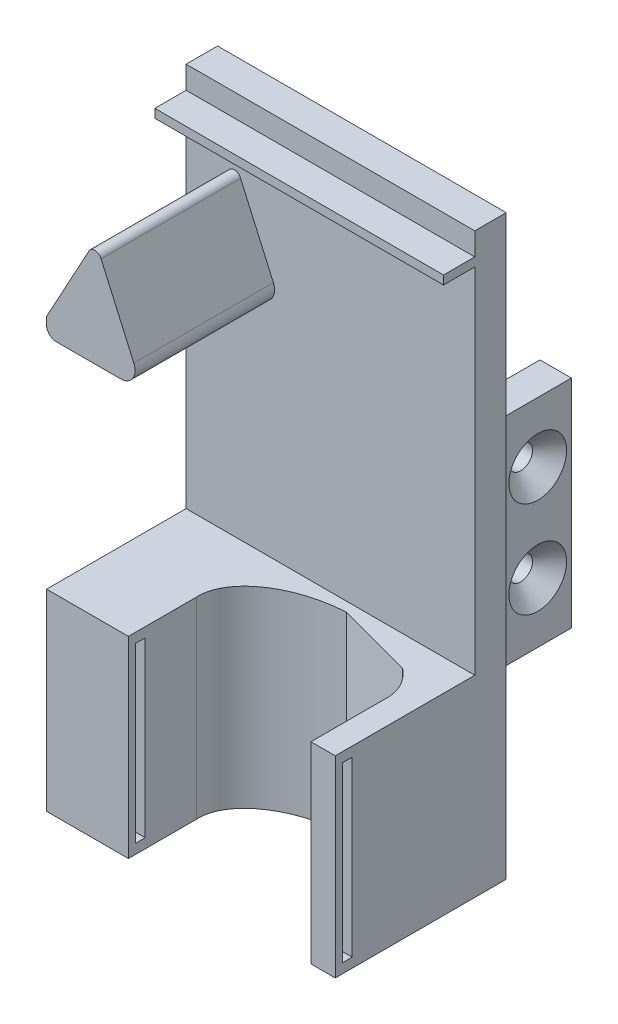
SolidWorks part; units mm, degrees
ref_plane "Front Plane" through (0, 0, 0) normal (0, 0, 1) x (1, 0, 0)
ref_plane "Top Plane" through (0, 0, 0) normal (0, 1, 0) x (1, 0, 0)
ref_plane "Right Plane" through (0, 0, 0) normal (1, 0, 0) x (0, 0, -1)
sketch "Sketch1" plane through (0, 0, 0) normal (0, 0, 1) x (1, 0, 0)
  line L1 (-30, 60) -> (30, 60)
  line L2 (-30, 60) -> (-30, -60)
  line L3 (-30, -60) -> (30, -60)
  line L4 (30, 60) -> (30, -60)
  line L5 (-30, 60) -> (30, -60) construction
  line L6 (-30, -60) -> (30, 60) construction
  point P0 (0, 0)
  dimension "D1" = 60
  dimension "D2" = 120
extrude "Boss-Extrude1" add sketch "Sketch1" along normal blind 6.54
sketch "Sketch7" plane through (0, 0, 6.54) normal (0, 0, 1) x (1, 0, 0)
  line L0 (-10, 25.5339) -> (-18.6733, 45.1016)
  line L1 (-30, 25.5339) -> (-10, 25.5339)
  line L6 (30, -60) -> (30, 60) construction
  line L15 (-21.3057, 45.0714) -> (-30, 29.1154)
  line L16 (-30, 60) -> (-30, -60) construction
  line L18 (-30, 29.1154) -> (-30, 25.5339)
  line L19 (30, 60) -> (-30, 60) construction
  arc A1 (-21.3057, 45.0714) -> (-18.6733, 45.1016) centre (-19.9839, 44.595) cw
  point P3 (-20, 46)
  dimension "D1" = 14
  dimension "D3" = 20
  dimension "D4" = 40
  dimension "D2" = 50
sketch "Sketch10" plane through (0, 0, 0) normal (0, 0, -1) x (-1, 0, 0)
  line L1 (20, 20) -> (26.54, 20)
  line L2 (-20, -25) -> (-20, 20)
  line L4 (-20, 20) -> (-26.54, 20)
  line L7 (20, -25) -> (20, 20)
  line L10 (-26.54, 20) -> (-26.54, -25)
  line L11 (-26.54, -25) -> (-20, -25)
  line L12 (26.54, 20) -> (26.54, -25)
  line L13 (26.54, -25) -> (20, -25)
  dimension "D1" = 6.54
  dimension "D2" = 20
  dimension "D3" = 6.54
  dimension "D4" = 20
  dimension "D5" = 45
  dimension "D6" = 45
extrude "Boss-Extrude5" add sketch "Sketch10" along normal blind 17
sketch "Sketch17" plane through (0, 0, 6.54) normal (0, 0, 1) x (1, 0, 0)
  line L0 (-30, 60) -> (-30, -60) construction
  line L1 (-30, -20) -> (30, -20)
  line L2 (-30, -20) -> (-30, -60)
  line L3 (-30, -60) -> (30, -60)
  line L4 (30, -20) -> (30, -60)
  line L5 (30, -60) -> (30, 60) construction
  line L6 (-30, -60) -> (30, -60) construction
  line L7 (30, 60) -> (-30, 60) construction
  dimension "D1" = 40
  dimension "D2" = 0
  dimension "D3" = 80
extrude "Boss-Extrude6" add sketch "Sketch17" along normal blind 29
sketch "Sketch18" plane through (0, -20, 0) normal (0, 1, 0) x (1, 0, 0)
  line L0 (5.335, -8.5264) -> (21.2913, -12.8258)
  line L1 (30, -35.54) -> (30, -6.54) construction
  line L2 (30, -35.54) -> (-30, -35.54) construction
  ellipse E0 centre (5.9723, -20.3092) end of major axis (24.9445, -19.283) minor radius 11.8 (5.335, -8.5264) -> (21.2913, -12.8258) ccw
  dimension "D1" = 43
  dimension "D2" = 5.0555
  dimension "D3" = 3.448
extrude "Cut-Extrude1" cut sketch "Sketch18" against normal up to next contours E0 L0
sketch "Sketch21" plane through (0, 0, 35.54) normal (0, 0, 1) x (1, 0, 0)
  line L0 (30, -20) -> (-30, -20) construction
  line L1 (-13, -20) -> (24.9445, -20)
  line L2 (-13, -20) -> (-13, -60)
  line L3 (-13, -60) -> (24.9445, -60)
  line L4 (24.9445, -20) -> (24.9445, -60)
  line L5 (-30, -60) -> (30, -60) construction
  line L6 (30, -60) -> (30, -20) construction
  dimension "D1" = 5.0555
  dimension "D2" = 43
extrude "Cut-Extrude2" cut sketch "Sketch21" against normal up to next contours L2 L3 L4 L1
sketch "Sketch23" plane through (-13, 0, 0) normal (1, 0, 0) x (0, 0, -1)
  line L0 (-35.54, -20) -> (-35.54, -60) construction
  line L1 (-34.04, -22) -> (-32.04, -22)
  line L2 (-34.04, -22) -> (-34.04, -58)
  line L3 (-34.04, -58) -> (-32.04, -58)
  line L4 (-32.04, -22) -> (-32.04, -58)
  line L5 (-21.3353, -60) -> (-35.54, -60) construction
  line L6 (-21.3353, -20) -> (-35.54, -20) construction
  dimension "D1" = 3.5
  dimension "D2" = 2
  dimension "D3" = 2
  dimension "D4" = 2
  dimension "D5" = 36
extrude "Cut-Extrude3" cut sketch "Sketch23" against normal blind 9
sketch "Sketch24" plane through (24.9445, 0, 0) normal (-1, 0, 0) x (0, 0, 1)
  line L0 (20.076, -60) -> (35.54, -60) construction
  line L1 (32.04, -22) -> (34.04, -22)
  line L2 (32.04, -22) -> (32.04, -58)
  line L3 (32.04, -58) -> (34.04, -58)
  line L4 (34.04, -22) -> (34.04, -58)
  line L5 (20.076, -20) -> (35.54, -20) construction
  line L6 (35.54, -20) -> (35.54, -60) construction
  dimension "D1" = 2
  dimension "D2" = 2
  dimension "D3" = 2
  dimension "D4" = 3.5
extrude "Cut-Extrude4" cut sketch "Sketch24" against normal blind 9
hole_wizard "CSK for M3 Flat Head Machine Screw4" positions "3DSketch2" profile "Sketch27" countersink size "M3" standard "ANSI Metric" end condition up to next
sketch3d "3DSketch2"
  line L4 (26.54, -25, -17) -> (26.54, -25, 0) construction
  line L6 (26.54, 20, -17) -> (26.54, 20, 0) construction
  line L7 (30, -60, 0) -> (30, 60, 0) construction
  line L8 (26.54, 20, 0) -> (26.54, -25, 0) construction
  point P14 (26.54, -12.5, -10)
  point P26 (26.54, 7.5, -10)
  dimension "D1" = 10
  dimension "D5" = 10.5817
  dimension "D2" = 12.5
  dimension "D3" = 12.5
  dimension "D4" = 10
sketch "Sketch27" plane through (26.54, -12.5, -10) normal (0, 1, 0) x (0, 0, -1)
  line L0 (0, 0) -> (0, 6.54)
  line L1 (0, 6.54) -> (2.465, 6.54)
  line L2 (2.465, 6.54) -> (2.465, 3.535)
  line L3 (2.465, 3.535) -> (6, 0)
  line L5 (6, 0) -> (0, 0)
  line L6 (-2.465, 3.535) -> (-6, 0) construction
  line L11 (0, -6.35) -> (0, 107.95) construction
  dimension "Thru Hole Dia." = 4.93
  dimension "Thru Hole Depth" = 6.54
  dimension "Near C'Sink Dia." = 12
  dimension "Near C'Sink Angle" = 90
hole_wizard "CSK for M3 Flat Head Machine Screw5" positions "3DSketch3" profile "Sketch29" countersink size "M3" standard "ANSI Metric" end condition up to next
sketch3d "3DSketch3"
  line L2 (-26.54, 20, -17) -> (-26.54, 20, 0) construction
  line L3 (-26.54, -25, -17) -> (-26.54, -25, 0) construction
  line L4 (-26.54, -25, 0) -> (-26.54, 20, 0) construction
  point P10 (-26.54, -12.5, -10)
  point P13 (-26.54, 7.5, -10)
  dimension "D1" = 10
  dimension "D3" = 12.5
  dimension "D2" = 10
  dimension "D4" = 12.5
sketch "Sketch29" plane through (-26.54, -12.5, -10) normal (0, 1, 0) x (0, 0, 1)
  line L0 (0, 0) -> (0, 6.54)
  line L1 (0, 6.54) -> (2.465, 6.54)
  line L2 (2.465, 6.54) -> (2.465, 3.535)
  line L3 (2.465, 3.535) -> (6, 0)
  line L5 (6, 0) -> (0, 0)
  line L6 (-2.465, 3.535) -> (-6, 0) construction
  line L11 (0, -6.35) -> (0, 107.95) construction
  dimension "Thru Hole Dia." = 4.93
  dimension "Thru Hole Depth" = 6.54
  dimension "Near C'Sink Dia." = 12
  dimension "Near C'Sink Angle" = 90
extrude "Boss-Extrude8" add sketch "Sketch7" along normal blind 29
sketch "Sketch36" plane through (0, 0, 6.54) normal (0, 0, 1) x (1, 0, 0)
  line L0 (-30, 53.5) -> (30, 53.5)
  line L1 (30, 60) -> (-30, 60) construction
  line L2 (-30, 60) -> (-30, 29.1154) construction
  line L3 (-30, 55.3) -> (30, 55.3)
  line L4 (30, -20) -> (30, 60) construction
  line L5 (-30, 55.3) -> (-30, 53.5)
  line L6 (30, 55.3) -> (30, 53.5)
  dimension "D1" = 6.5
  dimension "D2" = 4.7
extrude "Boss-Extrude9" add sketch "Sketch36" along normal blind 6.5
fillet "Fillet1" radius 3 1 edges at (-10, 25.5339, 21.04)
fillet "Fillet2" radius 2 1 edges at (-30, 25.5339, 21.04)
